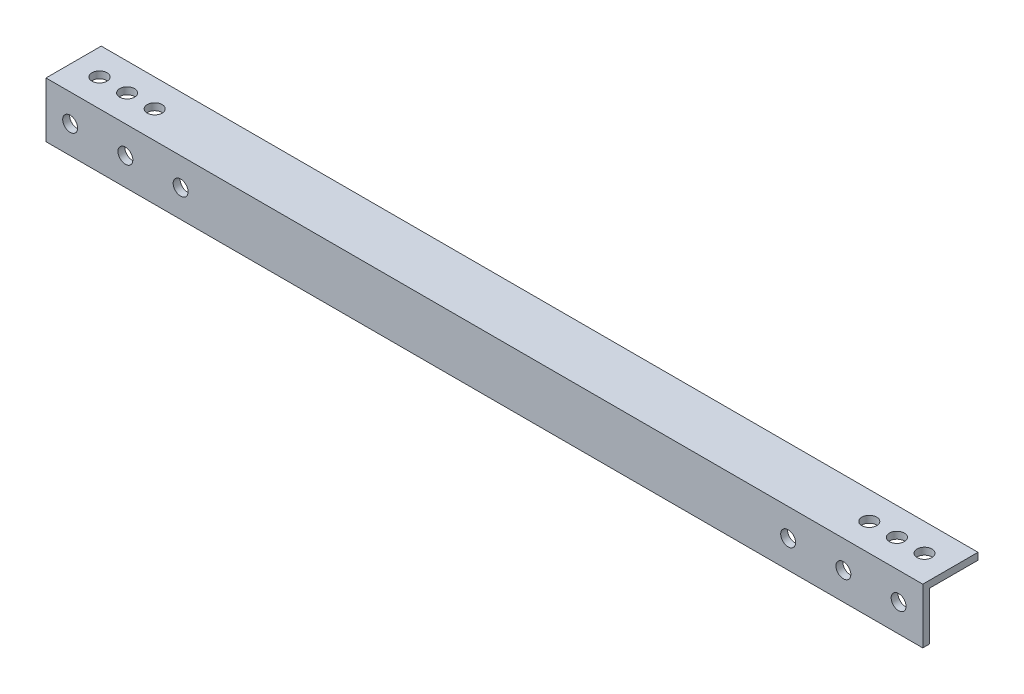
SolidWorks part; units mm, degrees
ref_plane "Front Plane" through (0, 0, 0) normal (0, 0, 1) x (1, 0, 0)
ref_plane "Top Plane" through (0, 0, 0) normal (0, 1, 0) x (1, 0, 0)
ref_plane "Right Plane" through (0, 0, 0) normal (1, 0, 0) x (0, 0, -1)
sketch "Sketch1" plane through (0, 0, 0) normal (1, 0, 0) x (0, 0, -1)
  line L0 (0, 0) -> (25.4, 0)
  line L2 (0, 0) -> (0, -25.4)
  line L4 (3.175, -3.175) -> (25.4, -3.175)
  line L5 (3.175, -3.175) -> (3.175, -25.4)
  line L6 (25.4, -3.175) -> (25.4, 0)
  line L7 (3.175, -25.4) -> (0, -25.4)
  line L8 (55, 0) -> (-55, 0) construction
  line L9 (0, 55) -> (0, -55) construction
  dimension "D1" = 25.4
  dimension "D2" = 25.4
  dimension "D4" = 3.175
  dimension "D3" = 3.175
extrude "Boss-Extrude1" add sketch "Sketch1" along normal blind 403.225
sketch "Sketch2" plane through (0, 0, 0) normal (0, 0, 1) x (1, 0, 0)
  line L0 (0, -12.7) -> (61.9125, -12.7) construction
  line L1 (0, -55) -> (0, 55) construction
  line L2 (403.225, -25.4) -> (0, -25.4) construction
  line L3 (0, 0) -> (0, -25.4) construction
  line L4 (201.6125, -25.4) -> (201.6125, 0) construction
  line L6 (403.225, 0) -> (0, 0) construction
  line L7 (403.225, -12.7) -> (341.3125, -12.7) construction
  circle A0 centre (11.1125, -12.7) radius 3.429
  circle A1 centre (36.5125, -12.7) radius 3.429
  circle A2 centre (61.9125, -12.7) radius 3.429
  circle A3 centre (341.3125, -12.7) radius 3.429
  circle A4 centre (366.7125, -12.7) radius 3.429
  circle A5 centre (392.1125, -12.7) radius 3.429
  dimension "D1" = 12.7
  dimension "D2" = 6.858
  dimension "D3" = 11.1125
  dimension "D5" = 25.4
  dimension "D4" = 3
extrude "Cut-Extrude1" cut sketch "Sketch2" against normal up to surface (3.175 mm away) up to face at (201.6125, -14.2875, -3.175)
sketch "Sketch3" plane through (0, 0, 0) normal (0, 1, 0) x (1, 0, 0)
  line L1 (0, -55) -> (0, 55) construction
  line L4 (201.6125, 25.4) -> (201.6125, 0) construction
  line L5 (403.225, 25.4) -> (0, 25.4) construction
  line L6 (403.225, 0) -> (0, 0) construction
  circle A0 centre (11.8999, 12.7) radius 3.429
  circle A1 centre (24.5999, 12.7) radius 3.429
  circle A2 centre (37.2999, 12.7) radius 3.429
  circle A3 centre (365.9251, 12.7) radius 3.429
  circle A4 centre (378.6251, 12.7) radius 3.429
  circle A5 centre (391.3251, 12.7) radius 3.429
  dimension "D1" = 6.858
  dimension "D2" = 11.8999
  dimension "D5" = 12.7
  dimension "D4" = 12.7
  dimension "D3" = 3
extrude "Cut-Extrude2" cut sketch "Sketch3" against normal up to surface (3.175 mm away) up to face at (201.6125, -3.175, -14.2875)
